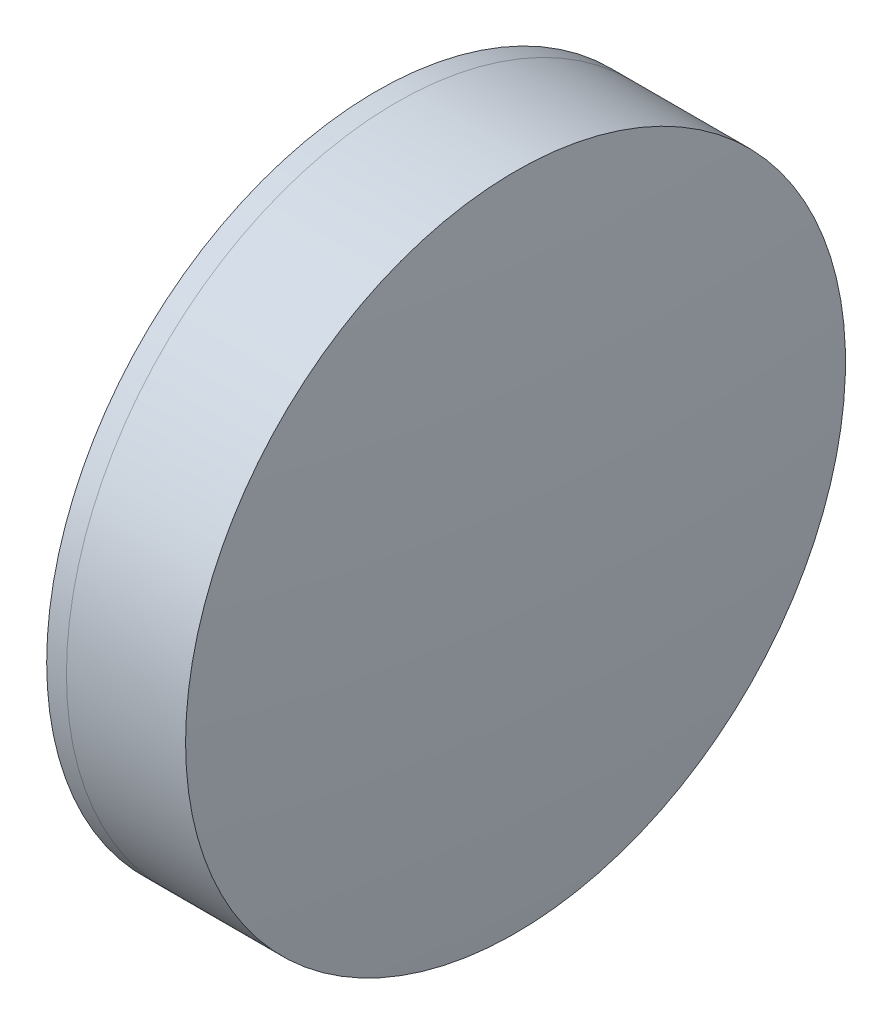
SolidWorks part; units mm, degrees
ref_plane "前视基准面" through (0, 0, 0) normal (0, 0, 1) x (1, 0, 0)
ref_plane "上视基准面" through (0, 0, 0) normal (0, 1, 0) x (1, 0, 0)
ref_plane "右视基准面" through (0, 0, 0) normal (1, 0, 0) x (0, 0, -1)
sketch "草图1" plane through (0, 0, 0) normal (0, 1, 0) x (1, 0, 0)
  line L0 (124.5233, 0) -> (395.1269, 0) construction
  line L1 (205.2882, -15) -> (206.1861, -15)
  line L2 (205.2882, 15) -> (206.1861, 15)
  arc A0 (206.1861, -15) -> (206.1861, 15) centre (180.9005, 0) ccw
  arc A1 (205.2882, 15) -> (205.2882, -15) centre (235.8005, 0) ccw
  point P4 (124.5233, 0)
  point P10 (201.8005, 0)
  point P11 (210.3005, 0)
  dimension "D3" = 34
  dimension "D4" = 29.4
  dimension "D1" = 15
  dimension "D2" = 15
  dimension "D5" = 8.5
revolve "旋转1" add sketch "草图1" angle 360 about L0
sketch "草图2" plane through (0, 0, 0) normal (0, 1, 0) x (1, 0, 0)
  line L0 (-0.5519, 0) -> (409.4962, 0) construction
  line L2 (206.1861, 15) -> (211.6024, 15)
  line L3 (206.1861, -15) -> (211.6024, -15)
  arc A0 (211.6024, -15) -> (211.6024, 15) centre (50.8005, 0) ccw
  arc A1 (206.1861, -15) -> (206.1861, 15) centre (180.9005, 0) ccw construction
  arc A2 (206.1861, -15) -> (206.1861, 15) centre (180.9005, 0) ccw
  point P4 (210.3005, 0)
  point P8 (212.3005, 0)
  dimension "D1" = 161.5
  dimension "D2" = 2
revolve "旋转3" add sketch "草图2" angle 360 about L0
